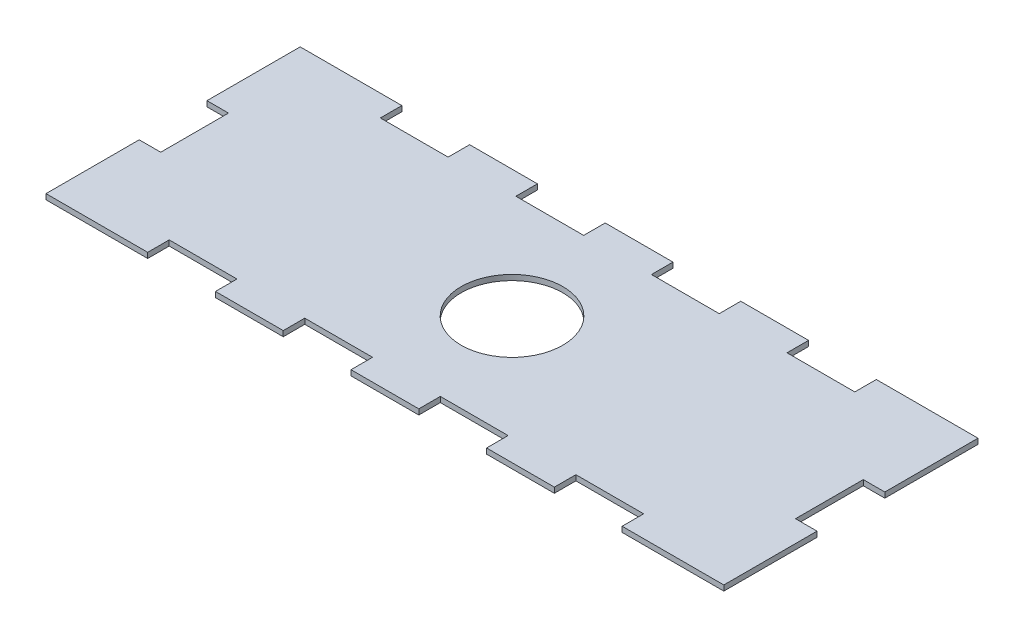
SolidWorks part; units mm, degrees
ref_plane "Front Plane" through (0, 0, 0) normal (0, 0, 1) x (1, 0, 0)
ref_plane "Top Plane" through (0, 0, 0) normal (0, 1, 0) x (1, 0, 0)
ref_plane "Right Plane" through (0, 0, 0) normal (1, 0, 0) x (0, 0, -1)
sketch "Sketch1" plane through (0, 0, 0) normal (0, 1, 0) x (1, 0, 0)
  line L0 (0, 37.5) -> (200, 37.5) construction
  line L1 (0, 0) -> (200, 0)
  line L2 (0, 0) -> (0, 75)
  line L3 (0, 75) -> (200, 75)
  line L4 (200, 0) -> (200, 75)
  line L5 (100, 0) -> (100, 75) construction
  line L6 (70, 0) -> (70, 6.35)
  line L7 (30, 0) -> (50, 0)
  line L8 (30, 0) -> (30, 6.35)
  line L9 (30, 6.35) -> (50, 6.35)
  line L10 (50, 0) -> (50, 6.35)
  line L11 (70, 0) -> (90, 0)
  line L12 (90, 0) -> (90, 6.35)
  line L13 (70, 6.35) -> (90, 6.35)
  line L14 (110, 0) -> (110, 6.35)
  line L15 (110, 0) -> (130, 0)
  line L16 (130, 0) -> (130, 6.35)
  line L17 (110, 6.35) -> (130, 6.35)
  line L18 (150, 0) -> (150, 6.35)
  line L19 (150, 0) -> (170, 0)
  line L20 (170, 0) -> (170, 6.35)
  line L21 (150, 6.35) -> (170, 6.35)
  line L22 (150, 75) -> (170, 75)
  line L23 (170, 75) -> (170, 68.65)
  line L24 (150, 68.65) -> (170, 68.65)
  line L25 (150, 75) -> (150, 68.65)
  line L26 (110, 75) -> (130, 75)
  line L27 (130, 75) -> (130, 68.65)
  line L28 (110, 68.65) -> (130, 68.65)
  line L29 (110, 75) -> (110, 68.65)
  line L30 (70, 75) -> (90, 75)
  line L31 (90, 75) -> (90, 68.65)
  line L32 (70, 68.65) -> (90, 68.65)
  line L33 (70, 75) -> (70, 68.65)
  line L34 (30, 68.65) -> (50, 68.65)
  line L35 (50, 75) -> (50, 68.65)
  line L36 (30, 75) -> (50, 75)
  line L37 (30, 75) -> (30, 68.65)
  line L38 (200, 47.5) -> (193.65, 47.5)
  line L43 (0, 27.5) -> (6.35, 27.5)
  line L44 (0, 27.5) -> (0, 47.5)
  line L45 (0, 47.5) -> (6.35, 47.5)
  line L46 (6.35, 27.5) -> (6.35, 47.5)
  line L47 (193.65, 27.5) -> (193.65, 47.5)
  line L48 (200, 27.5) -> (193.65, 27.5)
  line L49 (200, 27.5) -> (200, 47.5)
  circle A0 centre (100, 37.5) radius 15
  dimension "D8" = 30
  dimension "D1" = 200
  dimension "D2" = 75
  dimension "D3" = 6.35
  dimension "D4" = 20
  dimension "D6" = 10
  dimension "D7" = 20
  dimension "D9" = 10
  dimension "D12" = 20
  dimension "D13" = 6.35
  dimension "D5" = 4
extrude "Boss-Extrude1" add sketch "Sketch1" along normal blind 1.5875
